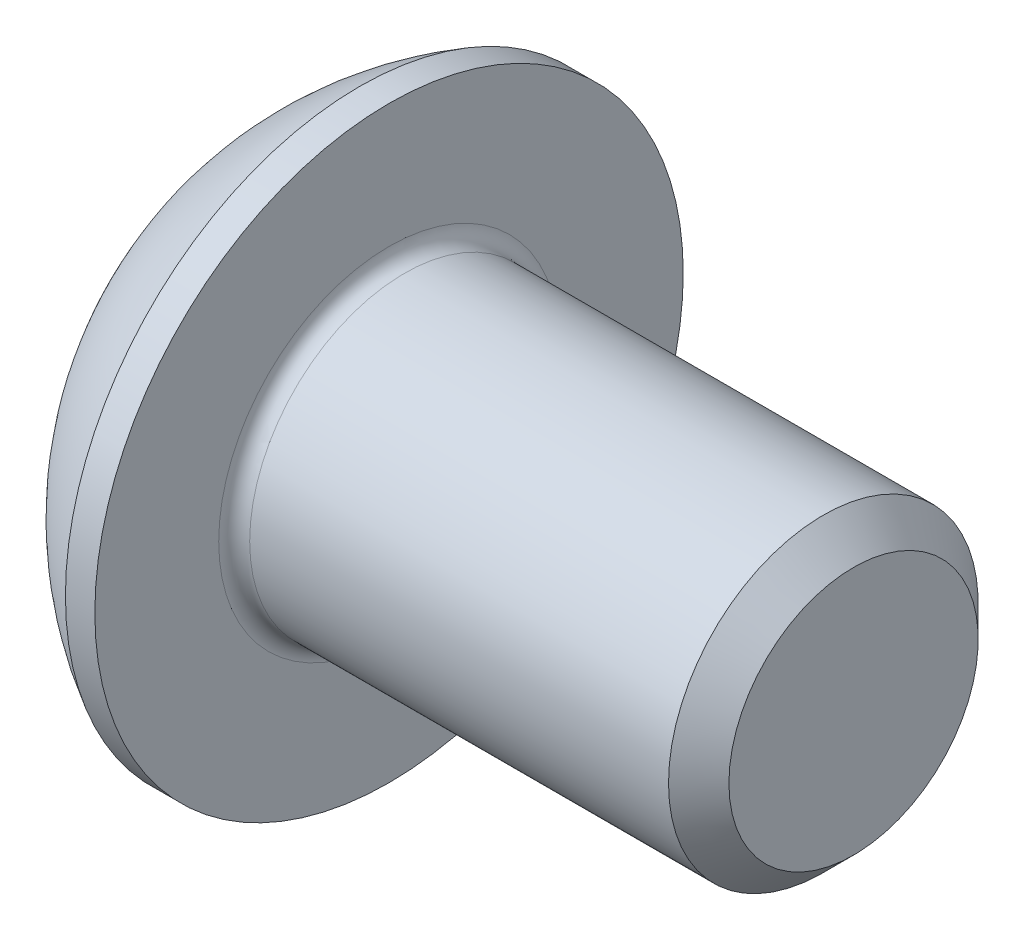
SolidWorks part; units mm, degrees
ref_plane "Plane1" through (0, 0, 0) normal (0, 0, 1) x (1, 0, 0)
ref_plane "Plane2" through (0, 0, 0) normal (0, 1, 0) x (1, 0, 0)
ref_plane "Plane3" through (0, 0, 0) normal (1, 0, 0) x (0, 0, -1)
sketch "BodySke" plane through (0, 0, 0) normal (0, 0, 1) x (1, 0, 0)
  line L0 (8.2, 0) -> (8.2, 1.61)
  line L1 (7.81, 2) -> (2.2, 2)
  line L2 (2.2, 2) -> (2.2, 3.8)
  line L3 (2.2, 3.8) -> (1.82, 3.8)
  line L4 (0, 0) -> (101.6, 0) construction
  line L5 (2.2, -3.8) -> (1.82, -3.8) construction
  line L6 (55.6768, -2) -> (2.2, -2) construction
  line L7 (8.2, 0) -> (0, 0)
  line L8 (0, 1.9) -> (0, -1.9) construction
  line L9 (0, 0) -> (0, 1.9)
  line L10 (8.2, 1.61) -> (7.81, 2)
  line L11 (8.2, -1.61) -> (7.81, -2) construction
  line L12 (2.9, 9.525) -> (2.9, -2) construction
  line L13 (2.2, 9.525) -> (2.2, -2) construction
  arc A1 (0, 1.9) -> (1.82, 3.8) centre (3.8853, 0) cw
  dimension "Diameter" = 4
  dimension "Length" = 6
  dimension "Head_dia" = 7.6
  dimension "D1" = 3.8
  dimension "Head_ht" = 2.2
  dimension "Head_side_ht" = 0.38
  dimension "Minor_dia" = 3.22
  dimension "Body_ch_ang" = 45
  dimension "Advance" = 0.7
  dimension "Thread_nom" = 6
revolve "BaseBody" add sketch "BodySke" angle 360 about L4
cosmetic thread "ThreadCosmetic" [suppressed] parameters "Thread_length"=4.6, "Thread_minor"=3.22
fillet "Fillet1" radius 0.2 1 edges at (2.2, 0, 2)
sketch "Sketch2" plane through (0, 0, 0) normal (0, 0, 1) x (1, 0, 0)
  line L0 (0, 1.25) -> (1.3, 1.25)
  line L1 (1.3, 1.25) -> (2.0217, 0)
  line L3 (2.0217, 0) -> (0, 0)
  line L4 (0, 0) -> (0, 1.25)
  line L5 (0, -1.25) -> (1.3, -1.25) construction
  line L6 (0, 0) -> (47.625, 0) construction
  dimension "D2" = 60
  dimension "PreBroach_depth" = 1.3
  dimension "PreBroach_dia" = 2.5
revolve "PreBroach" cut sketch "Sketch2" angle 360 about L6
sketch "Sketch3" plane through (0, 0, 0) normal (1, 0, 0) x (0, 0, -1)
  line L0 (-1.25, -0.7217) -> (-1.25, 0.7217)
  line L1 (-1.25, 0.7217) -> (0, 1.4434)
  line L2 (0, 1.4434) -> (1.25, 0.7217)
  line L3 (1.25, 0.7217) -> (1.25, -0.7217)
  line L4 (1.25, -0.7217) -> (0, -1.4434)
  line L5 (0, -1.4434) -> (-1.25, -0.7217)
  dimension "Hex_size" = 2.5
  dimension "D3" = 2.5
  dimension "D1" = 1.25
  dimension "D2" = 1.25
extrude "Hex" cut sketch "Sketch3" along normal blind 1.3
sketch "ThdSchSke" plane through (0, 0, 0) normal (0, 0, 1) x (1, 0, 0)
  line L0 (3.6, -1.61) -> (3.3269, -2)
  line L1 (3.6, -1.61) -> (3.8731, -2)
  line L2 (3.8731, -2) -> (3.8731, -2.5)
  line L3 (-3.175, 0) -> (5.1513, 0) construction
  line L5 (3.8731, -2.5) -> (3.3269, -2.5)
  line L6 (3.3269, -2.5) -> (3.3269, -2)
  dimension "Diameter" = 4
  dimension "Thread_minor" = 3.22
  dimension "SideAngle" = 55
  dimension "VeeAngle" = 70
  dimension "Overcut" = 5
  dimension "Start" = 3.6
revolve "ThreadSchematic" [suppressed] cut sketch "ThdSchSke" angle 360 about L3
pattern_linear "ThdSchPat" [suppressed]
equation "\"D1@BodySke\" = \"Head_dia@BodySke\" * .5"
equation "\"Thread_minor@ThreadCosmetic\" = \"Minor_dia@BodySke\""
equation "\"D1@Sketch3\" = \"Hex_size@Sketch3\" / 2"
equation "\"D2@Sketch3\" = \"D1@Sketch3\""
equation "\"D3@Sketch3\" = \"Hex_size@Sketch3\""
equation "\"Thread_length@ThreadCosmetic\" = ((sgn( (\"Length@BodySke\" - \"Advance@BodySke\" * 2.0) - \"Thread_nom@BodySke\" )-1)*( (\"Length@BodySke\" - \"Advance@BodySke\" * 2.0) - \"Thread_nom@BodySke\" ))/-2+ \"Thread_nom@BodySke\""
equation "\"Thread_minor@ThdSchSke\" = \"Minor_dia@BodySke\""
equation "\"Diameter@ThdSchSke\" = \"Diameter@BodySke\""
equation "\"Overcut@ThdSchSke\" = \"Diameter@BodySke\" * 1.25"
equation "\"Start@ThdSchSke\" = \"Head_ht@BodySke\" + \"Length@BodySke\" - \"Thread_length@ThreadCosmetic\"  '---Non-countersunk---"
equation "\"Num_threads@ThdSchPat\" = int( \"Thread_length@ThreadCosmetic\" / \"Advance@BodySke\" + 0.999 )  + 1"
equation "\"Advance@ThdSchPat\" = \"Thread_length@ThreadCosmetic\" /  (\"Num_threads@ThdSchPat\" - 1) 'relax it"
equation "\"Num_threads@ThdSchPat\" = \"Num_threads@ThdSchPat\" - sgn( \"Num_threads@ThdSchPat\" - 1) '---chamfered tips only---"
